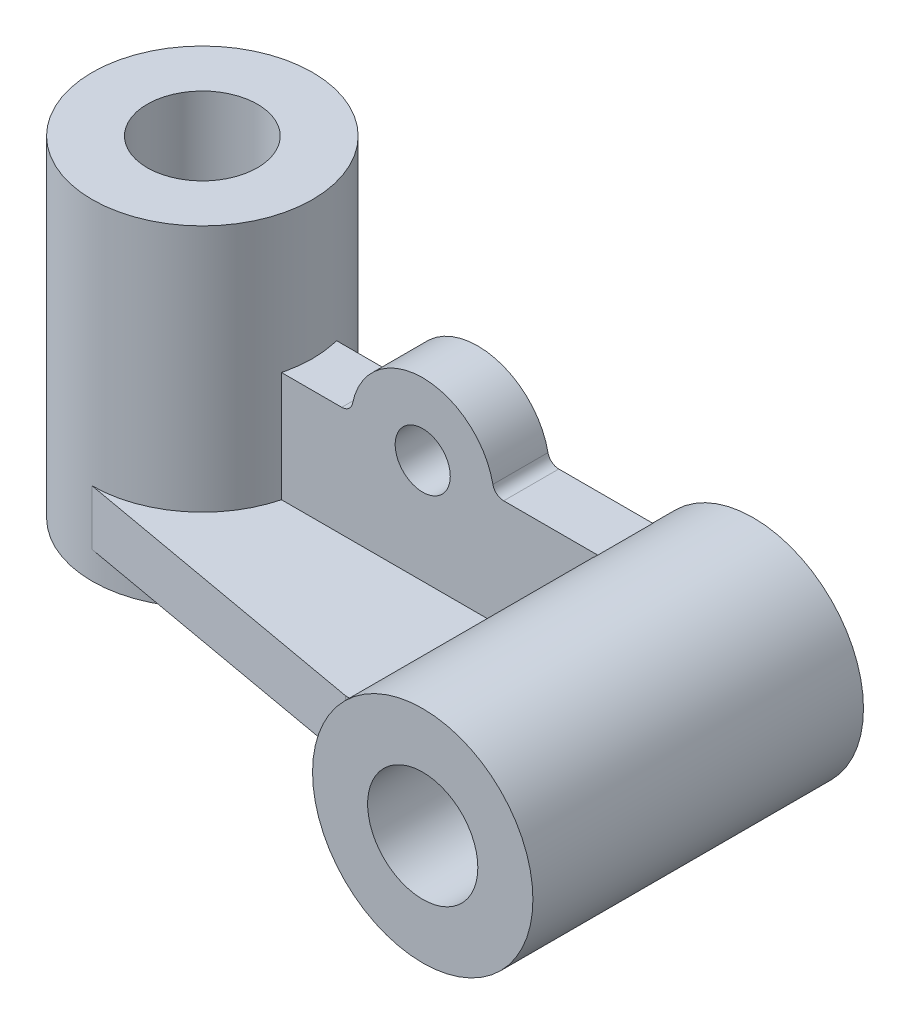
SolidWorks part; units mm, degrees
ref_plane "Front Plane" through (0, 0, 0) normal (0, 0, 1) x (1, 0, 0)
ref_plane "Top Plane" through (0, 0, 0) normal (0, 1, 0) x (1, 0, 0)
ref_plane "Right Plane" through (0, 0, 0) normal (1, 0, 0) x (0, 0, -1)
sketch "Sketch1" plane through (0, 0, 0) normal (0, 0, 1) x (1, 0, 0)
  line L0 (0, 26.3972) -> (0, -38.4527) construction
  line L1 (-53.3487, 0) -> (45.0346, 0) construction
  line L2 (0, 30) -> (0, -30)
  line L3 (0, -30) -> (20, -30)
  line L4 (20, -30) -> (20, 30)
  line L5 (20, 30) -> (0, 30)
  dimension "D1" = 60
  dimension "D2" = 20
revolve "cyl-purple" add sketch "Sketch1" angle 360 about L2
sketch "Sketch2" plane through (0, 30, 0) normal (0, 1, 0) x (1, 0, 0)
  circle A0 centre (0, 0) radius 10
  dimension "D1" = 20
extrude "Cut-Extrude1" cut sketch "Sketch2" against normal through all
ref_plane "Plane2" through (0, 0, 50) normal (0, 0, 1) x (1, 0, 0)
sketch "Sketch3" plane through (0, 0, 50) normal (0, 0, 1) x (1, 0, 0)
  line L0 (-26.6236, 0) -> (142.7461, 0) construction
  line L1 (0, 53.1866) -> (0, -50.2505) construction
  line L2 (90, 47.9131) -> (90, -59.9766) construction
  line L3 (0, -30) -> (191.1627, -30) construction
  line L4 (-20, -30) -> (20, -30) construction
  circle A0 centre (90, -10) radius 20
  circle A1 centre (90, -10) radius 10
  dimension "D1" = 40
  dimension "D2" = 20
  dimension "D3" = 90
extrude "cyl-blue" add sketch "Sketch3" against normal blind 60 separate body
ref_plane "Plane3" through (0, 0, -5) normal (0, 0, 1) x (1, 0, 0)
sketch "Sketch4" plane through (0, 0, -5) normal (0, 0, 1) x (1, 0, 0)
  line L0 (-19.6228, -30) -> (145.0037, -30) construction
  line L1 (-20, -30) -> (20, -30) construction
  line L2 (0, 39.5007) -> (0, -49.1941) construction
  line L4 (-38.69, -15) -> (133.7763, -15) construction
  line L5 (10, -15) -> (70.6351, -15)
  line L6 (10, 5) -> (30.3031, 5)
  line L8 (10, 5) -> (10, -15)
  line L9 (59.6969, 5) -> (76.7712, 5)
  circle A0 centre (90, -10) radius 20 construction
  arc A1 (70.6351, -15) -> (76.7712, 5) centre (90, -10) cw
  circle A4 centre (90, -10) radius 10 construction
  arc A7 (32.2627, 6.6) -> (57.7373, 6.6) centre (45, 4) cw
  circle A8 centre (45, 4) radius 5
  arc A9 (59.6969, 5) -> (57.7373, 6.6) centre (59.6969, 7) cw
  arc A10 (30.3031, 5) -> (32.2627, 6.6) centre (30.3031, 7) ccw
  dimension "D2" = 13
  dimension "D3" = 10
  dimension "D4" = 45
  dimension "D5" = 2
  dimension "D8" = 10
  dimension "D9" = 19
  dimension "D1" = 20
  dimension "D6" = 15
  dimension "D7" = 20
extrude "base-yellow" add sketch "Sketch4" along normal blind 10 separate body
ref_plane "Plane4" through (0, -25, 0) normal (0, 1, 0) x (1, 0, 0)
sketch "Sketch6" plane through (0, -25, 0) normal (0, 1, 0) x (1, 0, 0)
  line L0 (0, 35.6481) -> (0, 20) construction
  line L1 (-44.6641, 0) -> (126.7478, 0) construction
  line L8 (0, 0) -> (0, -43.6764) construction
  line L13 (110, -50) -> (110, -74.8178) construction
  line L14 (0, -20) -> (56, -30)
  line L17 (10, -5) -> (70.6351, -5) construction
  line L19 (19.3649, -5) -> (77.3091, -5)
  line L21 (56, -30) -> (77.3091, -30)
  line L22 (77.3091, -30) -> (77.3091, -5)
  circle A2 centre (0, 0) radius 20 construction
  arc A3 (0, -20) -> (19.3649, -5) centre (0, 0) ccw
  point P6 (70, -30)
  dimension "D1" = 25
  dimension "D2" = 56
  dimension "D3" = 14
  dimension "D4" = 77.3091
extrude "base-red" add sketch "Sketch6" along normal blind 10 separate body
